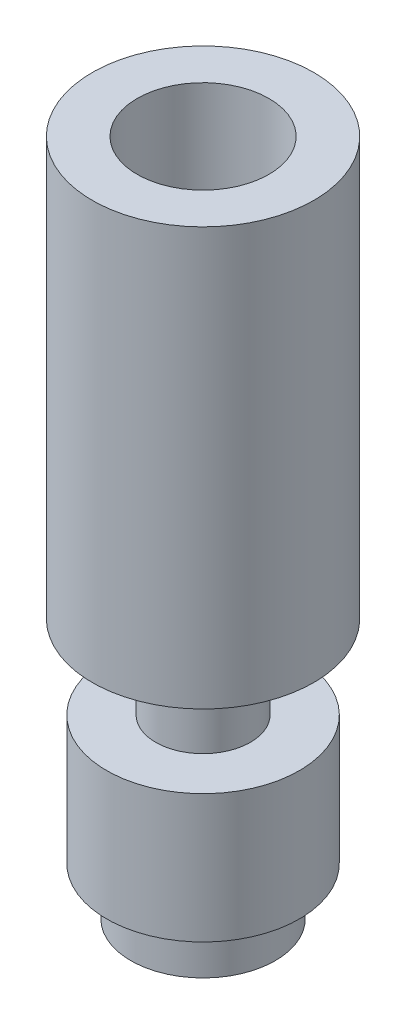
SolidWorks part; units mm, degrees
material "AISI 316 Stainless Steel Sheet (SS)"
ref_plane "Front Plane" through (0, 0, 0) normal (0, 0, 1) x (1, 0, 0)
ref_plane "Top Plane" through (0, 0, 0) normal (0, 1, 0) x (1, 0, 0)
ref_plane "Right Plane" through (0, 0, 0) normal (1, 0, 0) x (0, 0, -1)
sketch "Sketch2" plane through (0, 0, 0) normal (0, 0, 1) x (1, 0, 0)
  line L0 (0, 0) -> (0, 21.1) construction
  line L1 (-1, 0) -> (-2.25, 0)
  line L2 (-2.25, 0) -> (-2.25, 1.5)
  line L3 (-2.25, 1.5) -> (-3, 1.5)
  line L4 (-3, 1.5) -> (-3, 5.5)
  line L5 (-3, 5.5) -> (-1.475, 5.5)
  line L6 (-1.475, 5.5) -> (-1.475, 8.1)
  line L7 (-1.475, 8.1) -> (-3.45, 8.1)
  line L8 (-3.45, 8.1) -> (-3.45, 21.1)
  line L9 (-1, 0) -> (-1, 16.5417)
  line L10 (-1, 16.5417) -> (-2.05, 17.1)
  line L11 (-2.05, 17.1) -> (-2.05, 21.1)
  line L12 (-2.05, 21.1) -> (-3.45, 21.1)
  line L13 (-2.05, 21.1) -> (0, 21.1) construction
  dimension "D2" = 1.5
  dimension "D3" = 4.5
  dimension "D4" = 6
  dimension "D5" = 2.95
  dimension "D6" = 2
  dimension "D7" = 118
  dimension "D8" = 4
  dimension "D9" = 13
  dimension "D10" = 15.6
  dimension "D11" = 21.1
  dimension "D12" = 4.1
  dimension "D13" = 6.9
revolve "Revolve1" add sketch "Sketch2" angle 360 about L0
